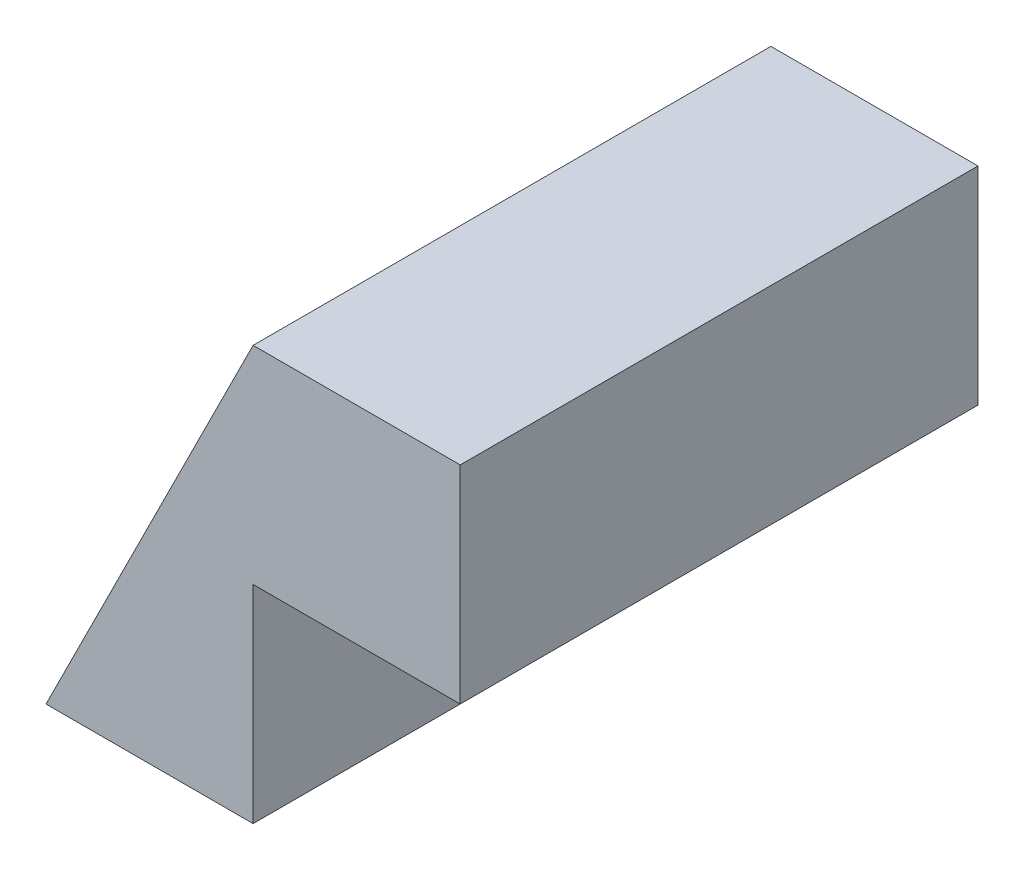
SolidWorks part; units mm, degrees
ref_plane "Front Plane" through (0, 0, 0) normal (0, 0, 1) x (1, 0, 0)
ref_plane "Top Plane" through (0, 0, 0) normal (0, 1, 0) x (1, 0, 0)
ref_plane "Right Plane" through (0, 0, 0) normal (1, 0, 0) x (0, 0, -1)
sketch "Sketch1" plane through (0, 0, 0) normal (0, 0, 1) x (1, 0, 0)
  line L0 (-20, -10) -> (-10, 10)
  line L1 (-10, 10) -> (0, 10)
  line L2 (0, 10) -> (0, 0)
  line L3 (0, 0) -> (-10, 0)
  line L4 (-10, 0) -> (-10, -10)
  line L5 (-10, -10) -> (-20, -10)
  dimension "D1" = 10
  dimension "D2" = 10
  dimension "D3" = 10
  dimension "D4" = 10
  dimension "D5" = 10
extrude "Boss-Extrude1" add sketch "Sketch1" along normal blind 25
